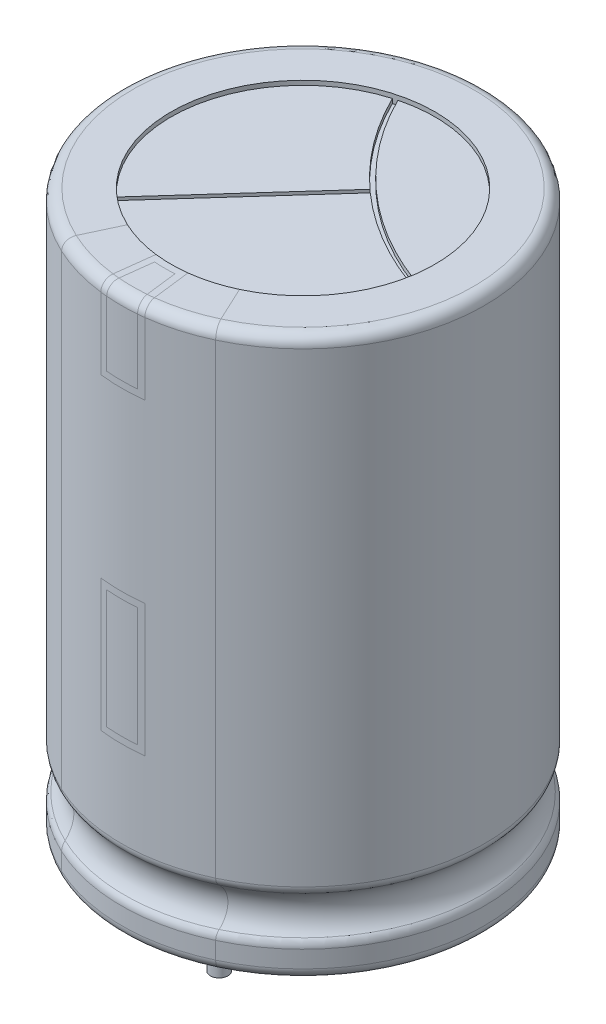
SolidWorks part; units mm, degrees
ref_plane "Płaszczyzna przednia" through (0, 0, 0) normal (0, 0, 1) x (1, 0, 0)
ref_plane "Płaszczyzna górna" through (0, 0, 0) normal (0, 1, 0) x (1, 0, 0)
ref_plane "Płaszczyzna prawa" through (0, 0, 0) normal (1, 0, 0) x (0, 0, -1)
sketch "Szkic1" plane through (0, 0, 0) normal (1, 0, 0) x (0, 0, -1)
  line L0 (0, 0) -> (7.75, 0)
  line L1 (8.25, 0.5) -> (8.25, 1.2753)
  line L2 (7.75, 25.4) -> (0, 25.4)
  line L3 (0, 25.4) -> (0, 0)
  line L4 (8.25, 3.7247) -> (8.25, 24.9)
  arc A0 (8.1071, 1.6252) -> (8.1071, 3.3748) centre (9, 2.5) cw
  arc A1 (7.75, 0) -> (8.25, 0.5) centre (7.75, 0.5) ccw
  arc A2 (8.25, 24.9) -> (7.75, 25.4) centre (7.75, 24.9) ccw
  arc A3 (8.1071, 1.6252) -> (8.25, 1.2753) centre (7.75, 1.2753) cw
  arc A4 (8.1071, 3.3748) -> (8.25, 3.7247) centre (7.75, 3.7247) ccw
  point P7 (8.25, 0)
  dimension "D2" = 0.5
  dimension "D3" = 8.1071
  dimension "D5" = 1.2753
  dimension "D1" = 1.25
  dimension "D4" = 8.25
  dimension "D10" = 25.4
revolve "Obrót1" add sketch "Szkic1" angle 360 about L3
sketch "Szkic2" plane through (0, 25.4, 0) normal (0, 1, 0) x (1, 0, 0)
  circle A0 centre (0, 0) radius 6
  circle A1 centre (0, 0) radius 7.75 construction
  dimension "D1" = 12
extrude "Wytnij-wyciągnięcie1" cut sketch "Szkic2" against normal blind 0.2
sketch "Szkic3" plane through (0, 25.2, 0) normal (0, 1, 0) x (1, 0, 0)
  line L1 (1.3684, 1.6706) -> (-4.0866, -4.3932)
  line L2 (1.5171, 1.5368) -> (-3.9379, -4.5269)
  arc A0 (-1.4988, 5.8098) -> (5.9354, -0.8781) centre (10.605, 11.7886) ccw
  arc A1 (-1.6951, 5.7556) -> (1.3684, 1.6706) centre (10.605, 11.7886) ccw
  arc A2 (-1.4988, 5.8098) -> (-1.6951, 5.7556) centre (0, 0) ccw
  circle A3 centre (0, 0) radius 6 construction
  arc A5 (5.9022, -1.0789) -> (5.9354, -0.8781) centre (0, 0) ccw
  arc A6 (-4.0866, -4.3932) -> (-3.9379, -4.5269) centre (0, 0) ccw
  arc A7 (1.5171, 1.5368) -> (5.9022, -1.0789) centre (10.605, 11.7886) ccw
  dimension "D1" = 13.5
  dimension "D3" = 6
  dimension "D2" = 13.7
  dimension "D4" = 1.3684
  dimension "D5" = 1.5171
  dimension "D6" = 5.9022
  dimension "D7" = 5.9354
  dimension "D8" = 3.9379
extrude "Wytnij-wyciągnięcie2" cut sketch "Szkic3" against normal blind 0.2
sketch "Szkic4" plane through (0, 0, 0) normal (0, -1, 0) x (1, 0, 0)
  circle A0 centre (0, 0) radius 6
  dimension "D1" = 12
extrude "Wytnij-wyciągnięcie3" cut sketch "Szkic4" against normal blind 0.5
sketch "Szkic5" plane through (0, 0, 0) normal (0, 0, 1) x (1, 0, 0)
  line L0 (0, 0) -> (3.5, 0)
  line L1 (3.5, 0) -> (3.5, 25.4)
  line L2 (-3.5, 25.4) -> (3.5, 25.4)
  line L3 (-3.5, 25.4) -> (-3.5, 0)
  line L4 (-3.5, 0) -> (0, 0)
  line L5 (-0.7, 7.95) -> (0.7, 7.95)
  line L6 (0.7, 7.95) -> (0.7, 13.35)
  line L7 (-0.7, 13.35) -> (0.7, 13.35)
  line L8 (-0.7, 7.95) -> (-0.7, 13.35)
  line L9 (-0.7, 25.4) -> (-0.7, 21.95)
  line L10 (-0.7, 21.95) -> (0.7, 21.95)
  line L11 (-1, 7.65) -> (1, 7.65)
  line L12 (-1, 7.65) -> (-1, 13.65)
  line L13 (-1, 13.65) -> (1, 13.65)
  line L14 (1, 7.65) -> (1, 13.65)
  line L15 (-1, 25.4) -> (-1, 21.65)
  line L16 (-1, 21.65) -> (1, 21.65)
  line L17 (1, 21.65) -> (1, 25.4)
  line L18 (0.7, 21.95) -> (0.7, 25.4)
  dimension "D1" = 0.7
  dimension "D2" = 3.5
  dimension "D3" = 7.65
  dimension "D4" = 7.95
  dimension "D5" = 13.35
  dimension "D6" = 21.65
  dimension "D7" = 0.7
  dimension "D8" = 25.4
split line "Linia podziałowa1"
sketch "Szkic8" plane through (0, 0, 0) normal (0, 1, 0) x (1, 0, 0)
  line L6 (-1, -8.1892) -> (-0.7273, -5.9558)
  line L9 (0.7273, -5.9558) -> (1, -8.1892)
  line L10 (-0.7021, -8.2256) -> (-0.4648, -6.2828)
  line L11 (0.4648, -6.2828) -> (0.7021, -8.2256)
  line L14 (3.5, -7.4708) -> (2.5455, -5.4333)
  line L15 (-3.5, -7.4708) -> (-2.5455, -5.4333)
  arc A0 (2.5455, -5.4333) -> (0.7273, -5.9558) centre (0, 0) cw
  arc A1 (-0.4648, -6.2828) -> (0.4648, -6.2828) centre (0, 0) ccw
  arc A2 (-0.7273, -5.9558) -> (-2.5455, -5.4333) centre (0, 0) cw
  arc A3 (-3.5, -7.4708) -> (-1, -8.1892) centre (0, 0) ccw
  arc A5 (-0.7014, -8.2201) -> (0.7014, -8.2201) centre (0, 0) ccw
  arc A7 (1, -8.1892) -> (3.5, -7.4708) centre (0, 0) ccw
  dimension "D1" = 6
  dimension "D2" = 6.3
  dimension "D3" = 8.25
  dimension "D4" = 0.4648
  dimension "D7" = 0.7273
  dimension "D5" = 0.7014
  dimension "D6" = 0.7021
  dimension "D8" = 2.5455
split line "Linia podziałowa2"
sketch "Szkic9" plane through (0, 0, 0) normal (0, 1, 0) x (1, 0, 0)
  line L0 (0.6227, -7.5744) -> (0.4286, -5.9847)
  line L4 (-0.6227, -7.5744) -> (-0.4286, -5.9847)
  line L8 (-3.5, -7.4708) -> (-2.5455, -5.4333)
  line L9 (3.5, -7.4708) -> (2.5455, -5.4333)
  line L10 (0.9576, -7.8418) -> (0.7273, -5.9558)
  line L11 (-0.9576, -7.8418) -> (-0.7273, -5.9558)
  arc A0 (-3.5, -7.4708) -> (3.5, -7.4708) centre (0, 0) ccw
  arc A1 (-2.5455, -5.4333) -> (2.5455, -5.4333) centre (0, 0) ccw
  arc A2 (-0.9576, -7.8418) -> (0.9576, -7.8418) centre (0, 0) ccw
  arc A3 (-0.6227, -7.5744) -> (0.6227, -7.5744) centre (0, 0) ccw
  dimension "D1" = 8.25
  dimension "D2" = 6
  dimension "D7" = 0.7273
  dimension "D3" = 7.9
  dimension "D4" = 7.6
  dimension "D5" = 0.4286
  dimension "D6" = 0.6227
  dimension "D8" = 2.5455
split line "Linia podziałowa3"
sketch "Szkic10" plane through (0, 0.5, 0) normal (0, -1, 0) x (-1, 0, 0)
  line L0 (0, 0) -> (0, -3.81) construction
  line L1 (0, 0) -> (0, 3.81) construction
  circle A0 centre (0, -3.81) radius 0.4
  circle A1 centre (0, 3.81) radius 0.4
  dimension "D3" = 0.8
  dimension "D1" = 3.81
  dimension "D2" = 3.81
extrude "Dodanie-wyciągnięcie1" add sketch "Szkic10" along normal blind 4 separate body
sketch "Szkic11" plane through (0, 0.5, 0) normal (0, -1, 0) x (-1, 0, 0)
  line L0 (-0.9341, -3.6289) -> (-1.2591, -4.5218)
  line L1 (-4.4371, -0.75) -> (4.4371, -0.75)
  line L2 (-4.4371, 0.75) -> (4.4371, 0.75)
  line L3 (0.9341, -3.6289) -> (1.2591, -4.5218)
  line L4 (1.2591, 4.5218) -> (0.9353, 3.6323)
  line L5 (-0.9315, 3.6307) -> (-1.2583, 4.5237)
  arc A0 (5.1923, 1.8138) -> (2.3531, 4.9712) centre (0, 0) ccw
  arc A1 (-5.1923, -1.8138) -> (-2.3531, -4.9712) centre (0, 0) ccw
  arc A2 (0.9341, -3.6289) -> (-0.9341, -3.6289) centre (0, -3.9689) ccw
  arc A3 (0.9353, 3.6323) -> (-0.9315, 3.6307) centre (0.0016, 3.9721) cw
  arc A4 (-2.3516, 4.9719) -> (-5.1923, 1.8138) centre (0, 0) ccw
  arc A5 (2.3531, -4.9712) -> (5.1923, -1.8138) centre (0, 0) ccw
  circle A6 centre (0, 0) radius 6 construction
  arc A7 (4.4371, -0.75) -> (5.1923, -1.8138) centre (4.4371, -1.55) cw
  arc A8 (4.4371, 0.75) -> (5.1923, 1.8138) centre (4.4371, 1.55) ccw
  arc A9 (1.2591, 4.5218) -> (2.3531, 4.9712) centre (2.0108, 4.2481) cw
  arc A10 (-1.2583, 4.5237) -> (-2.3516, 4.9719) centre (-2.0095, 4.2487) ccw
  arc A11 (-5.1923, 1.8138) -> (-4.4371, 0.75) centre (-4.4371, 1.55) ccw
  arc A12 (-5.1923, -1.8138) -> (-4.4371, -0.75) centre (-4.4371, -1.55) cw
  arc A13 (-1.2591, -4.5218) -> (-2.3531, -4.9712) centre (-2.0108, -4.2481) cw
  arc A14 (1.2591, -4.5218) -> (2.3531, -4.9712) centre (2.0108, -4.2481) ccw
  dimension "D1" = 5.5
  dimension "D2" = 0.994
  dimension "D3" = 0.9936
  dimension "D9" = 0.9315
  dimension "D4" = 0.8
  dimension "D5" = 0.7513
  dimension "D6" = 0.9341
  dimension "D7" = 1.2591
  dimension "D8" = 4.4371
extrude "Dodanie-wyciągnięcie2" add sketch "Szkic11" along normal blind 1.2 separate body
sketch "Szkic12" plane through (0, -0.7, 0) normal (0, -1, 0) x (-1, 0, 0)
  circle A0 centre (0, 0) radius 4
  circle A1 centre (0, 0) radius 3
  dimension "D1" = 8
  dimension "D2" = 6
extrude "Wytnij-wyciągnięcie4" cut sketch "Szkic12" against normal blind 0.3
fillet "Zaokrąglenie1" radius 0.05 16 edges at (1.14, -0.7, 4.1946) (1.7068, -0.7, 4.9881) (4.0897, -0.7, 3.6776) (5.0894, -0.7, 1.0869) (4.1831, -0.7, 0.75) (2.925, -0.7, 2.7285) (1.9125, -0.7, 2.3113) (-1.9125, -0.7, 2.3113) (0, -0.7, 2.9749) (0, -0.7, 0.75) (-4.1831, -0.7, 0.75) (-5.0894, -0.7, 1.0869) (-4.0897, -0.7, 3.6776) (-1.7068, -0.7, 4.9881) (-1.14, -0.7, 4.1946) (-2.925, -0.7, 2.7285)
fillet "Zaokrąglenie2" radius 0.05 16 edges at (5.0894, -0.7, -1.0869) (4.0891, -0.7, -3.6782) (1.706, -0.7, -4.9889) (1.1383, -0.7, -4.1959) (2.9241, -0.7, -2.7295) (4.1831, -0.7, -0.75) (-1.7068, -0.7, -4.9881) (-4.0897, -0.7, -3.6776) (-5.0894, -0.7, -1.0869) (-4.1831, -0.7, -0.75) (-2.925, -0.7, -2.7285) (-1.14, -0.7, -4.1946) (-0.0012, -0.7, -2.9785) (1.9064, -0.7, -2.3164) (-1.9074, -0.7, -2.3156) (0, -0.7, -0.75)
